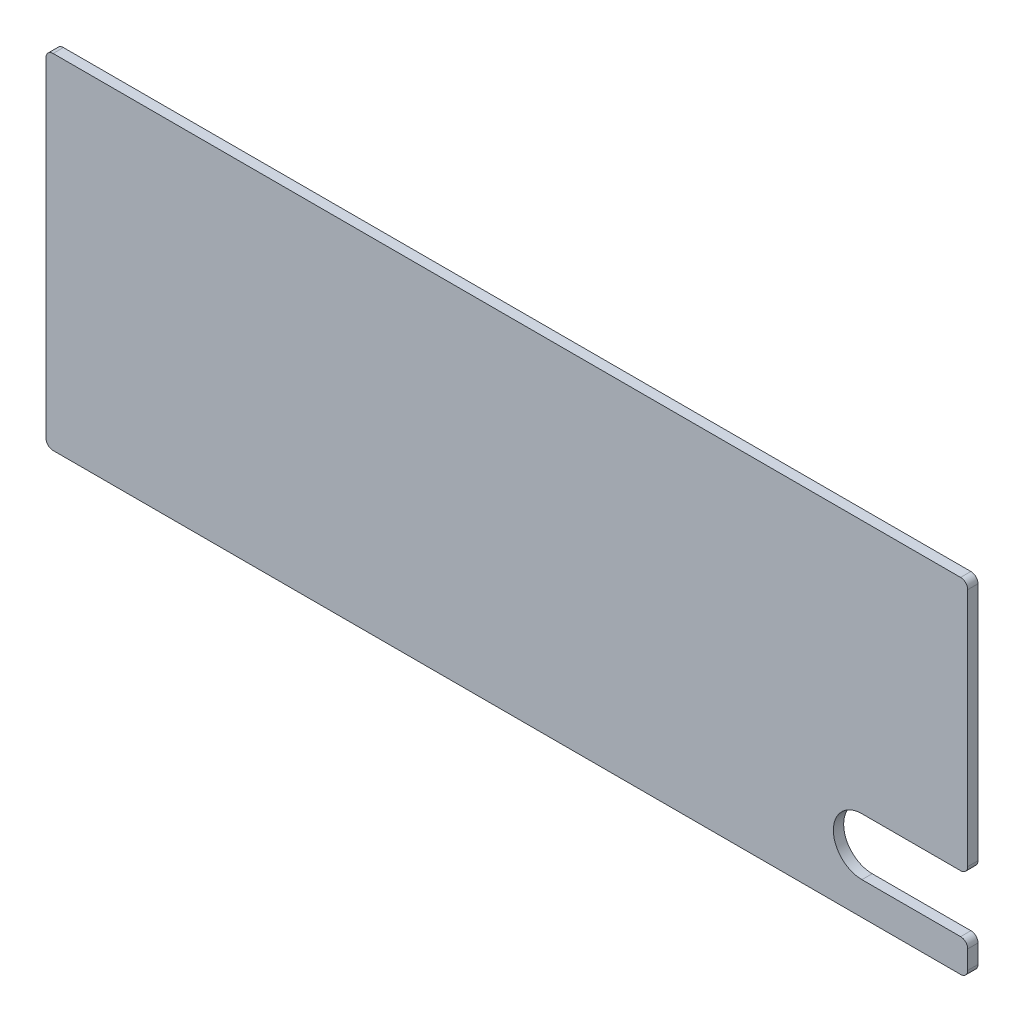
SolidWorks part; units mm, degrees
ref_plane "Piano frontale" through (0, 0, 0) normal (0, 0, 1) x (1, 0, 0)
ref_plane "Piano superiore" through (0, 0, 0) normal (0, 1, 0) x (1, 0, 0)
ref_plane "Piano destro" through (0, 0, 0) normal (1, 0, 0) x (0, 0, -1)
sketch "Schizzo1" plane through (0, 0, 0) normal (0, 0, 1) x (1, 0, 0)
  line L1 (0, 0) -> (130, 0)
  line L2 (0, 0) -> (0, 48.5)
  line L3 (0, 48.5) -> (130, 48.5)
  line L4 (130, 0) -> (130, 48.5)
  dimension "D1" = 130
  dimension "D2" = 48.5
extrude "Estrusione-Estrusione1" add sketch "Schizzo1" along normal blind 1.45
sketch "Schizzo2" plane through (0, 0, 1.45) normal (0, 0, 1) x (1, 0, 0)
  line L0 (144.9225, 8.6484) -> (115.0775, 8.6484) construction
  line L2 (144.9225, 4.6229) -> (115.0775, 4.6229)
  line L3 (144.9225, 12.6738) -> (115.0775, 12.6738)
  line L5 (130, 0) -> (130, 48.5) construction
  arc A0 (144.9225, 4.6229) -> (144.9225, 12.6738) centre (144.9225, 8.6484) ccw
  arc A1 (115.0775, 12.6738) -> (115.0775, 4.6229) centre (115.0775, 8.6484) ccw
  point P4 (130, 8.6484)
extrude "Taglio-Estrusione1" cut sketch "Schizzo2" against normal blind 12
fillet "Raccordo1" radius 1 6 edges at (130, 48.5, 0.725) (130, 12.6738, 0.725) (130, 0, 0.725) (130, 4.6229, 0.725) (0, 0, 0.725) (0, 48.5, 0.725)
